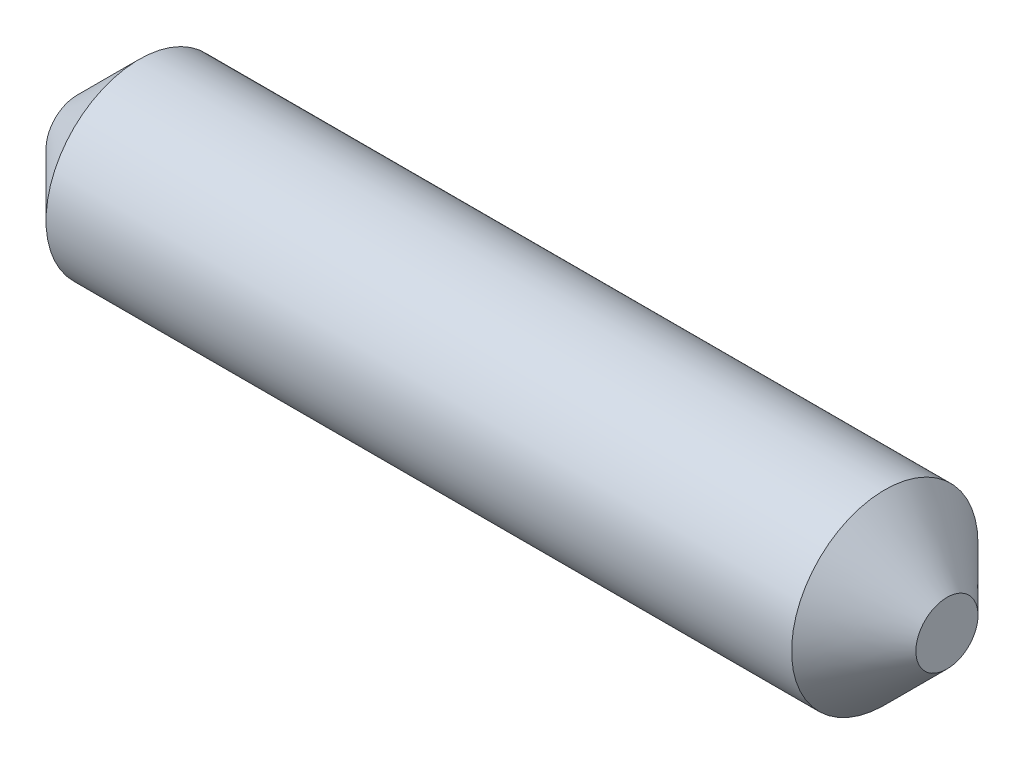
SolidWorks part; units mm, degrees
ref_plane "Płaszczyzna przednia" through (0, 0, 0) normal (0, 0, 1) x (1, 0, 0)
ref_plane "Płaszczyzna górna" through (0, 0, 0) normal (0, 1, 0) x (1, 0, 0)
ref_plane "Płaszczyzna prawa" through (0, 0, 0) normal (1, 0, 0) x (0, 0, -1)
sketch "Szkic1" plane through (0, 0, 0) normal (1, 0, 0) x (0, 0, -1)
  circle A0 centre (0, 0) radius 1.5
  dimension "D1" = 3
extrude "Dodanie-wyciągnięcie1" add sketch "Szkic1" along normal mid plane 14 contours A0
chamfer "Sfazowanie1" distance 1 angle 45 2 edges at (-7, 0, -1.5) (7, 0, -1.5)
